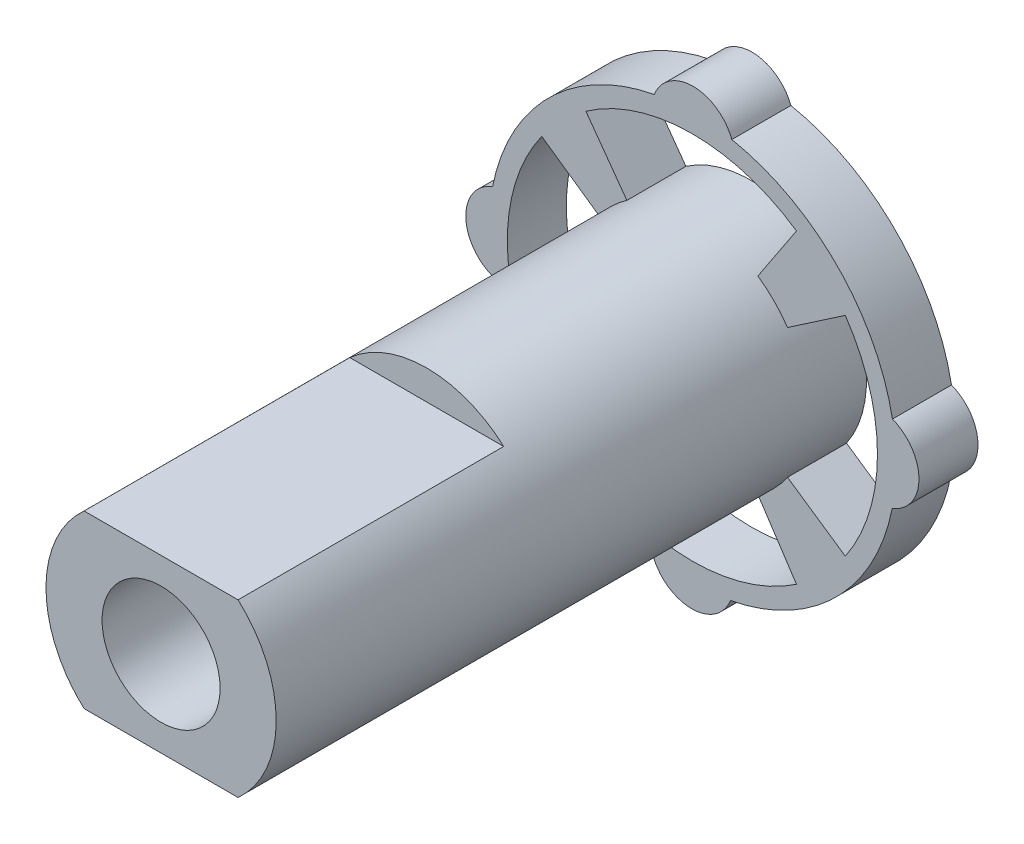
SolidWorks part; units mm, degrees
ref_plane "Front" through (0, 0, 0) normal (0, 0, 1) x (1, 0, 0)
ref_plane "Top" through (0, 0, 0) normal (0, 1, 0) x (1, 0, 0)
ref_plane "Right" through (0, 0, 0) normal (1, 0, 0) x (0, 0, -1)
sketch "草图1" plane through (0, 0, 0) normal (0, 0, 1) x (1, 0, 0)
  circle A0 centre (0, 0) radius 1
  circle A1 centre (0, 0) radius 1.95
  dimension "D1" = 2
  dimension "D2" = 3.9
extrude "凸台-拉伸1" add sketch "草图1" along normal mid plane 10
sketch "草图3" plane through (0, 0, -5) normal (0, 0, -1) x (-1, 0, 0)
  line L0 (0, 0) -> (3.7701, 3.7701) construction
  line L1 (0, 0) -> (-3.3847, -3.3847) construction
  line L2 (0, 0) -> (3.7387, -3.7387) construction
  line L3 (0, 0) -> (-3.3892, 3.3892) construction
  line L4 (0, 0) -> (3.5693, 2.4993) construction
  line L5 (0, 0) -> (2.3473, 3.3522) construction
  line L6 (0, 0) -> (-2.6781, 3.8248) construction
  line L7 (0, 0) -> (-3.8152, 2.6714) construction
  line L8 (0, 0) -> (-4.0414, -2.8298) construction
  line L9 (0, 0) -> (-2.6503, -3.785) construction
  line L10 (0, 0) -> (4.5573, -3.191) construction
  line L11 (0, 0) -> (2.6411, -3.7719) construction
  line L12 (2.5518, 1.8215) -> (1.58, 1.1428)
  line L13 (1.8041, 2.5642) -> (1.1096, 1.6035)
  line L14 (-1.7636, 2.5922) -> (-1.1096, 1.6035)
  line L15 (-2.5902, 1.7665) -> (-1.6111, 1.0985)
  line L16 (-2.5902, -1.7665) -> (-1.6111, -1.0985)
  line L17 (-1.7636, -2.5922) -> (-1.1096, -1.6035)
  line L18 (2.5902, -1.7665) -> (1.6111, -1.0985)
  line L19 (1.7636, -2.5922) -> (1.1096, -1.6035)
  arc A0 (-0.668, 3.3847) -> (-3.3892, 0.6448) centre (0, 0) ccw
  arc A1 (-0.668, 3.3847) -> (0.6448, 3.3892) centre (-0.0108, 3.1352) cw
  arc A2 (3.3847, 0.668) -> (3.3892, -0.6448) centre (3.1352, 0.0108) cw
  arc A3 (0.668, -3.3847) -> (-0.6448, -3.3892) centre (0.0108, -3.1352) cw
  arc A4 (-3.3847, -0.668) -> (-3.3892, 0.6448) centre (-3.1352, -0.0108) cw
  arc A5 (1.8041, 2.5642) -> (-1.7636, 2.5922) centre (0, 0) ccw
  arc A6 (-3.3847, -0.668) -> (-0.6448, -3.3892) centre (0, 0) ccw
  arc A7 (3.3847, 0.668) -> (0.6448, 3.3892) centre (0, 0) ccw
  arc A8 (0.668, -3.3847) -> (3.3892, -0.6448) centre (0, 0) ccw
  arc A9 (1.58, 1.1428) -> (1.1096, 1.6035) centre (0, 0) ccw
  arc A10 (-2.5902, 1.7665) -> (-2.5902, -1.7665) centre (0, 0) ccw
  arc A11 (-1.7636, -2.5922) -> (1.7636, -2.5922) centre (0, 0) ccw
  arc A12 (2.5902, -1.7665) -> (2.5518, 1.8215) centre (0, 0) ccw
  arc A13 (-1.1096, 1.6035) -> (-1.6111, 1.0985) centre (0, 0) ccw
  arc A14 (-1.6111, -1.0985) -> (-1.1096, -1.6035) centre (0, 0) ccw
  arc A15 (1.1096, -1.6035) -> (1.6111, -1.0985) centre (0, 0) ccw
  point P3 (0, 3.85)
  point P4 (0.6448, 3.3892)
  point P6 (1.8041, 2.5642)
  point P7 (-0.668, 3.3847)
  point P21 (0, 0)
  point P33 (2.2233, 2.2106)
  point P35 (1.1096, 1.6035)
  point P36 (2.5518, 1.8215)
  point P37 (1.58, 1.1428)
  point P38 (-1.1096, 1.6035)
  point P39 (-1.6111, 1.0985)
  point P40 (-1.7636, 2.5922)
  point P41 (-2.5902, 1.7665)
  point P42 (-2.5902, -1.7665)
  point P43 (-1.7636, -2.5922)
  point P44 (-1.1096, -1.6035)
  point P45 (-1.6111, -1.0985)
  point P46 (1.1096, -1.6035)
  point P47 (1.6111, -1.0985)
  point P48 (2.5902, -1.7665)
  point P49 (1.7636, -2.5922)
  dimension "D1" = 4
extrude "凸台-拉伸3" add sketch "草图3" against normal blind 1
sketch "草图5" plane through (0, 0, 5) normal (0, 0, 1) x (1, 0, 0)
  line L1 (-1.9918, 2.3559) -> (1.6945, 2.3559)
  line L2 (-1.9918, 2.3559) -> (-1.9918, 1.45)
  line L3 (-1.9918, 1.45) -> (1.6945, 1.45)
  line L4 (1.6945, 2.3559) -> (1.6945, 1.45)
  line L5 (-2.0725, -1.45) -> (2.3851, -1.45)
  line L6 (-2.0725, -1.45) -> (-2.0725, -2.9568)
  line L7 (-2.0725, -2.9568) -> (2.3851, -2.9568)
  line L8 (2.3851, -1.45) -> (2.3851, -2.9568)
  dimension "D1" = 1.45
  dimension "D2" = 1.45
extrude "切除-拉伸4" cut sketch "草图5" against normal blind 4.5
